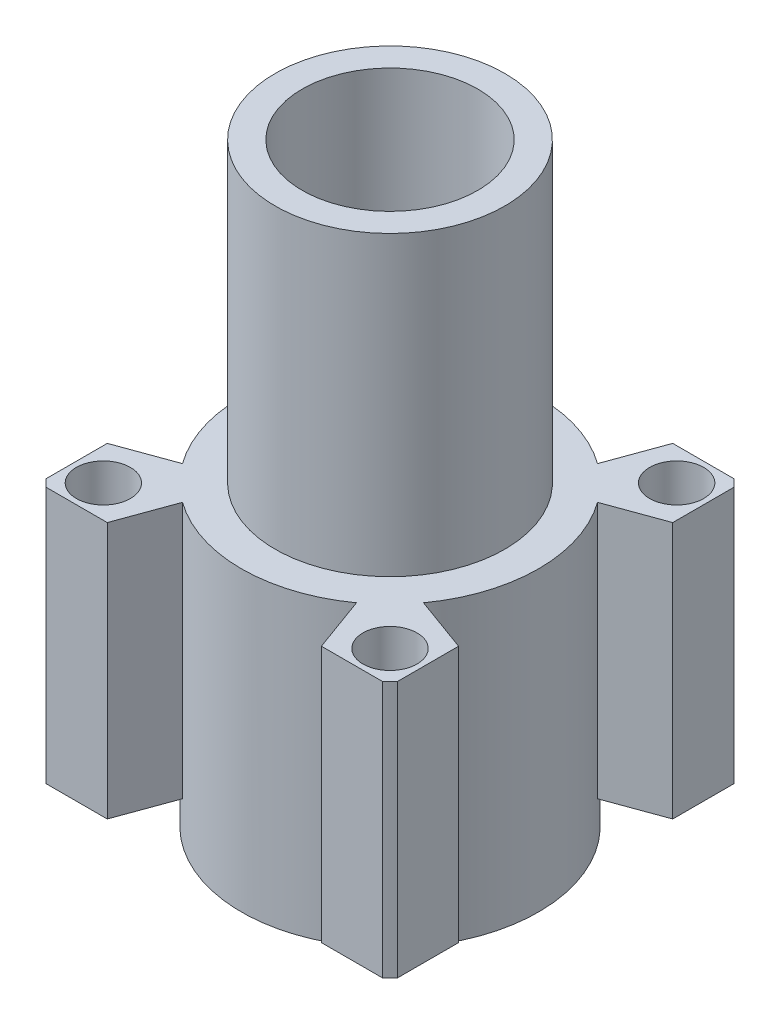
SolidWorks part; units mm, degrees
ref_plane "Plan de face" through (0, 0, 0) normal (0, 0, 1) x (1, 0, 0)
ref_plane "Plan de dessus" through (0, 0, 0) normal (0, 1, 0) x (1, 0, 0)
ref_plane "Plan de droite" through (0, 0, 0) normal (1, 0, 0) x (0, 0, -1)
sketch "Esquisse1" plane through (0, 0, 0) normal (0, 0, 1) x (1, 0, 0)
  line L0 (-6.5, 17) -> (-6.5, 41)
  line L1 (-11, 19) -> (-11, -3)
  line L2 (-11, -3) -> (-10, -3)
  line L3 (-10, -3) -> (-10, 17)
  line L4 (-8.5, 19) -> (-8.5, 41)
  line L5 (-10, 17) -> (-6.5, 17)
  line L6 (-11, 19) -> (-8.5, 19)
  line L7 (-8.5, 41) -> (-6.5, 41)
  line L8 (-11, 19) -> (-10, 19) construction
  line L9 (-10, 41) -> (-6.5, 41) construction
  line L10 (-11, 17) -> (-10, 17) construction
  line L12 (0, 0) -> (0, 14.9808) construction
  line L15 (-10, 17) -> (-6.5, 17) construction
  line L16 (-8.5, 0) -> (-8.5, 14.9808) construction
  line L18 (-6.5, 0) -> (-6.5, 14.9808) construction
revolve "Révolution1" add sketch "Esquisse1" angle 360 about L12
sketch "Esquisse3" plane through (0, 19, 0) normal (0, 1, 0) x (1, 0, 0)
  line L0 (-12.4499, -13) -> (-7.9241, -13)
  line L1 (12.4499, 13) -> (7.9241, 13)
  line L2 (13, 12.4499) -> (13, 7.9241)
  line L3 (-13, -12.4499) -> (-13, -7.9241)
  line L4 (0, 0) -> (0, 4.2793) construction
  line L5 (0, 0) -> (-3.606, 0) construction
  line L6 (8.9187, 6.4387) -> (13, 7.9241)
  line L7 (13, -7.9241) -> (13, -12.4499)
  line L8 (6.4387, -8.9187) -> (7.9241, -13)
  line L9 (-6.4387, -8.9187) -> (-7.9241, -13)
  line L10 (8.9187, -6.4387) -> (13, -7.9241)
  line L11 (-8.9187, -6.4387) -> (-13, -7.9241)
  line L12 (-8.9187, 6.4387) -> (-13, 7.9241)
  line L13 (-6.4387, 8.9187) -> (-7.9241, 13)
  line L14 (6.4387, 8.9187) -> (7.9241, 13)
  line L15 (-7.9241, 13) -> (-12.4499, 13)
  line L16 (-13, 7.9241) -> (-13, 12.4499)
  line L17 (7.9241, -13) -> (12.4499, -13)
  circle A0 centre (10.6066, 10.6066) radius 2
  arc A1 (8.9187, -6.4387) -> (8.9187, 6.4387) centre (0, 0) ccw
  circle A2 centre (-10.6066, -10.6066) radius 2
  circle A3 centre (-10.6066, 10.6066) radius 2
  circle A4 centre (10.6066, -10.6066) radius 2
  arc A5 (-13, -12.4499) -> (-12.4499, -13) centre (0, 0) ccw
  arc A6 (-12.4499, 13) -> (-13, 12.4499) centre (0, 0) ccw
  arc A7 (13, 12.4499) -> (12.4499, 13) centre (0, 0) ccw
  arc A8 (12.4499, -13) -> (13, -12.4499) centre (0, 0) ccw
  arc A9 (6.4387, 8.9187) -> (-6.4387, 8.9187) centre (0, 0) ccw
  arc A10 (-8.9187, 6.4387) -> (-8.9187, -6.4387) centre (0, 0) ccw
  circle A12 centre (0, 0) radius 10
  arc A13 (-6.4387, -8.9187) -> (6.4387, -8.9187) centre (0, 0) ccw
extrude "Extrusion2" add sketch "Esquisse3" against normal blind 19
